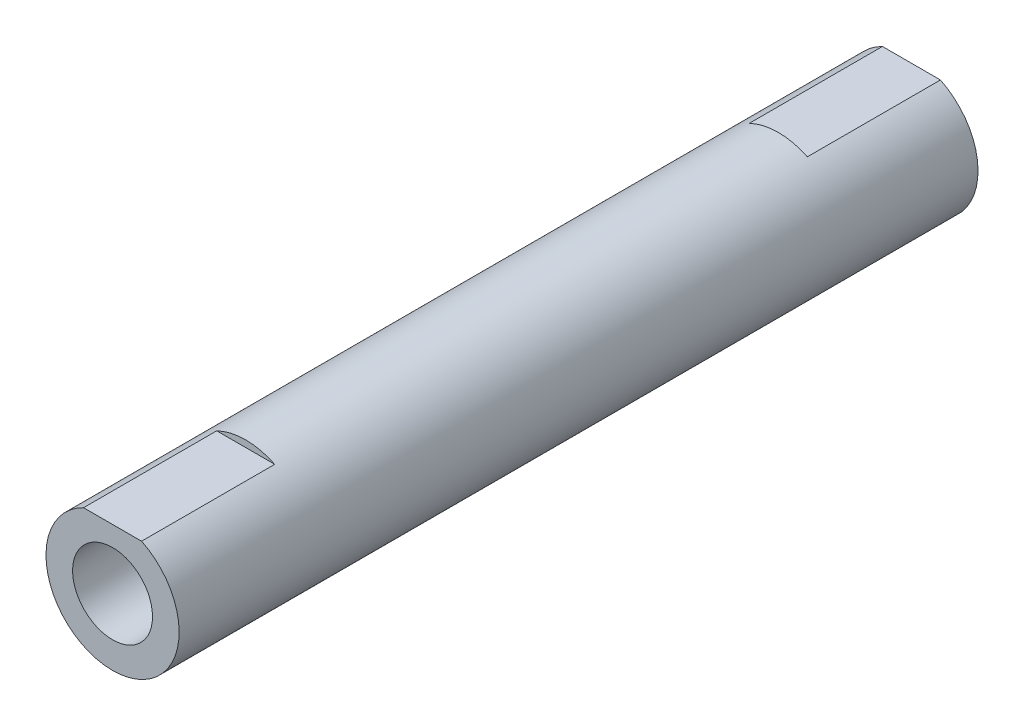
SolidWorks part; units mm, degrees
ref_plane "Front Plane" through (0, 0, 0) normal (0, 0, 1) x (1, 0, 0)
ref_plane "Top Plane" through (0, 0, 0) normal (0, 1, 0) x (1, 0, 0)
ref_plane "Right Plane" through (0, 0, 0) normal (1, 0, 0) x (0, 0, -1)
sketch "Sketch1" plane through (0, 0, 0) normal (0, 0, 1) x (1, 0, 0)
  circle A0 centre (0, 0) radius 3
  circle A1 centre (0, 0) radius 5
  dimension "D1" = 6
  dimension "D2" = 10
extrude "Boss-Extrude2" add sketch "Sketch1" along normal mid plane 60
sketch "Sketch7" plane through (0, 0, -30) normal (0, 0, -1) x (-1, 0, 0)
  line L0 (-2.1794, 4.5) -> (2.1794, 4.5)
  circle A0 centre (0, 0) radius 5 construction
  arc A1 (2.1794, 4.5) -> (-2.1794, 4.5) centre (0, 0) ccw
  dimension "D1" = 4.5
extrude "Cut-Extrude9" cut sketch "Sketch7" against normal blind 10
mirror "Mirror2" about plane through (0, 0, 0) normal (0, 0, 1) of "Cut-Extrude9"
